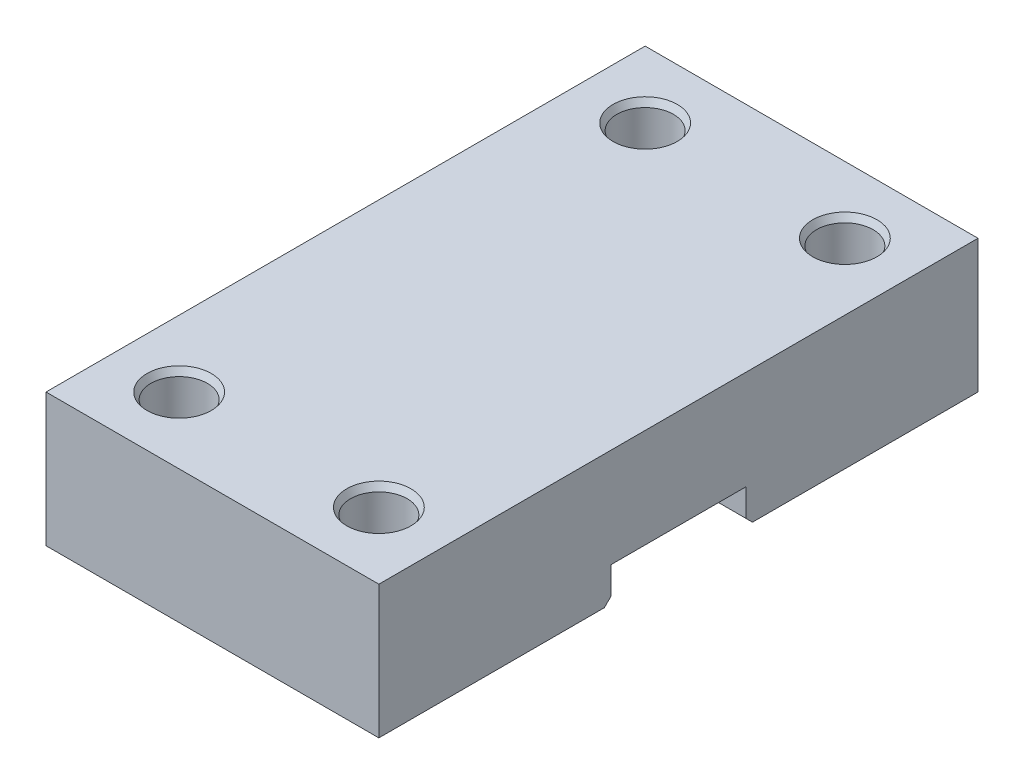
SolidWorks part; units mm, degrees
ref_plane "Спереди" through (0, 0, 0) normal (0, 0, 1) x (1, 0, 0)
ref_plane "Сверху" through (0, 0, 0) normal (0, 1, 0) x (1, 0, 0)
ref_plane "Справа" through (0, 0, 0) normal (1, 0, 0) x (0, 0, -1)
sketch "Sketch1" plane through (0, 0, 0) normal (0, 1, 0) x (1, 0, 0)
  line L1 (25, -45) -> (-25, -45)
  line L2 (25, -45) -> (25, 45)
  line L3 (25, 45) -> (-25, 45)
  line L4 (-25, -45) -> (-25, 45)
  line L5 (25, -45) -> (-25, 45) construction
  line L6 (25, 45) -> (-25, -45) construction
  point P0 (0, 0)
  dimension "D1" = 50
  dimension "D2" = 90
extrude "Boss-Extrude1" add sketch "Sketch1" along normal blind 20
sketch "Sketch2" plane through (25, 0, 0) normal (1, 0, 0) x (0, 0, -1)
  line L0 (0, 0) -> (0, 20) construction
  line L1 (-45, 0) -> (45, 0) construction
  line L2 (-45, 20) -> (45, 20) construction
  line L4 (10.125, 5.1) -> (-10.125, 5.1)
  line L5 (10.125, 5.1) -> (10.125, 0)
  line L6 (10.125, 0) -> (-10.125, 0)
  line L7 (-10.125, 5.1) -> (-10.125, 0)
  line L8 (10.125, 5.1) -> (-10.125, 0) construction
  line L9 (10.125, 0) -> (-10.125, 5.1) construction
  point P6 (0, 2.55)
  dimension "D1" = 20.25
  dimension "D2" = 5.1
extrude "Cut-Extrude1" cut sketch "Sketch2" against normal through all and the other way through all
sketch "Sketch3" plane through (0, 0, 0) normal (0, -1, 0) x (1, 0, 0)
  line L0 (-15, 35) -> (15, -35) construction
  line L1 (-15, -35) -> (15, 35) construction
  line L2 (0, 45) -> (0, -45) construction
  line L3 (25, 35) -> (-25, 35) construction
  line L4 (25, 45) -> (25, 10.125) construction
  line L5 (-25, 10.125) -> (-25, 45) construction
  line L6 (-25, -35) -> (25, -35) construction
  line L7 (-25, -45) -> (-25, -10.125) construction
  line L8 (25, -10.125) -> (25, -45) construction
  line L9 (-25, 45) -> (25, 45) construction
  line L10 (25, -45) -> (-25, -45) construction
  circle A0 centre (-15, 35) radius 4.25
  circle A1 centre (-15, -35) radius 4.25
  circle A2 centre (15, 35) radius 4.25
  circle A3 centre (15, -35) radius 4.25
  point P6 (0, 0)
  point P7 (0, 0)
  dimension "D1" = 8.5
  dimension "D2" = 30
  dimension "D3" = 70
extrude "Cut-Extrude2" cut sketch "Sketch3" against normal through all
chamfer "Chamfer1" distance 1 angle 30 4 edges at (-15, 20, -39.25) (15, 20, -39.25) (15, 20, 30.75) (-15, 20, 30.75)
chamfer "Chamfer2" distance 1 angle 45 2 edges at (0, 0, -10.125) (0, 0, 10.125)
